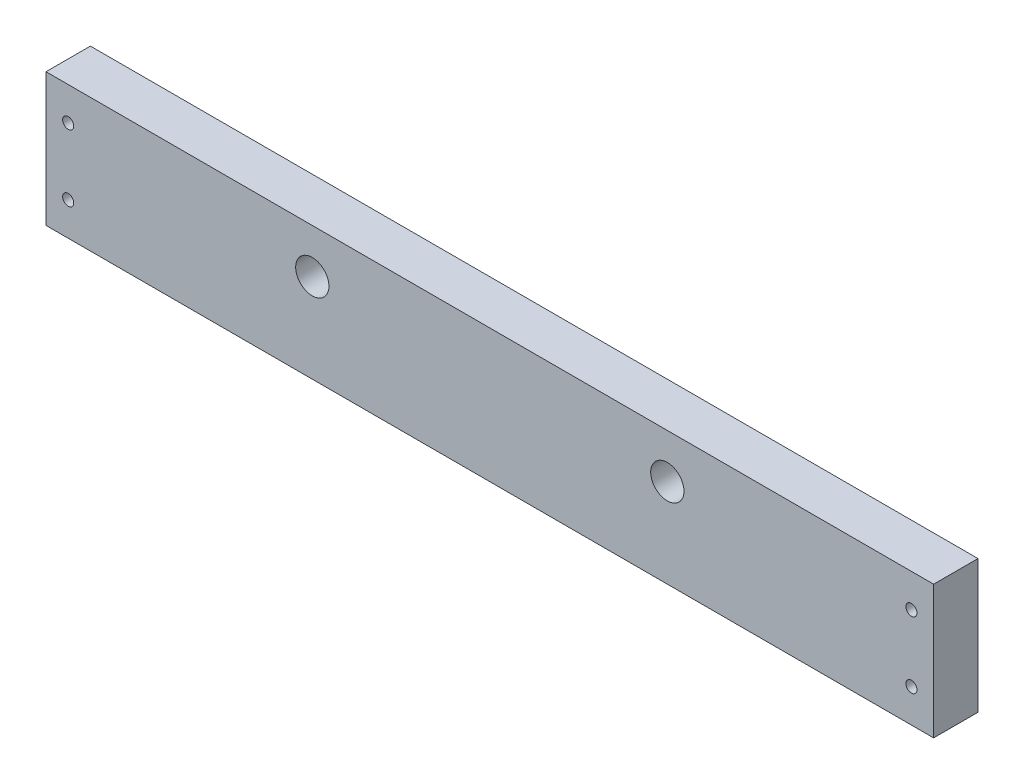
SolidWorks part; units mm, degrees
ref_plane "Front Plane" through (0, 0, 0) normal (0, 0, 1) x (1, 0, 0)
ref_plane "Top Plane" through (0, 0, 0) normal (0, 1, 0) x (1, 0, 0)
ref_plane "Right Plane" through (0, 0, 0) normal (1, 0, 0) x (0, 0, -1)
sketch "Sketch1" plane through (0, 0, 0) normal (0, 0, 1) x (1, 0, 0)
  line L0 (-127, 12.7) -> (127, 12.7)
  line L1 (127, 12.7) -> (127, -25.4)
  line L2 (127, -25.4) -> (-127, -25.4)
  line L3 (-127, -25.4) -> (-127, 12.7)
  circle A0 centre (-50.8, 0) radius 4.7625
  circle A1 centre (50.8, 0) radius 4.7625
  circle A2 centre (-120.65, 3.175) radius 1.5875
  circle A3 centre (-120.65, -15.875) radius 1.5875
  circle A4 centre (120.65, 3.175) radius 1.5875
  circle A5 centre (120.65, -15.875) radius 1.5875
  dimension "D1" = 2
extrude "Boss-Extrude1" add sketch "Sketch1" along normal blind 12.7
